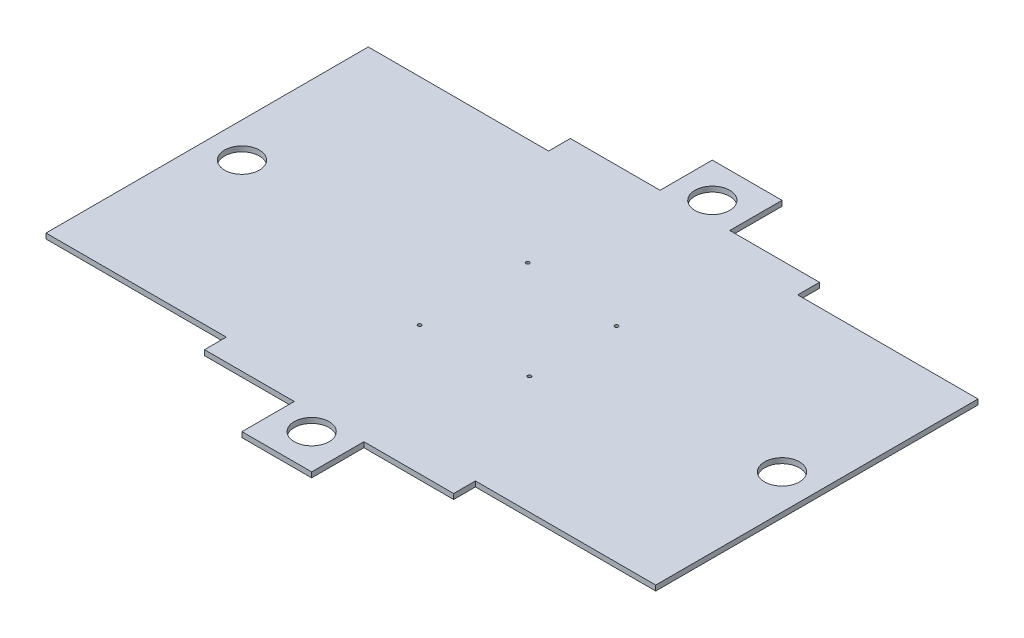
SolidWorks part; units mm, degrees
material "Acrylic (Medium-high impact)"
ref_plane "Front Plane" through (0, 0, 0) normal (0, 0, 1) x (1, 0, 0)
ref_plane "Top Plane" through (0, 0, 0) normal (0, 1, 0) x (1, 0, 0)
ref_plane "Right Plane" through (0, 0, 0) normal (1, 0, 0) x (0, 0, -1)
sketch "Sketch1" plane through (0, 0, 0) normal (0, 1, 0) x (1, 0, 0)
  line L4 (-111.7909, 69.7038) -> (-111.7909, 82.2038)
  line L5 (31.2091, 69.7038) -> (31.2091, 82.2038)
  line L8 (-111.7909, -115.2962) -> (-111.7909, -127.7962)
  line L9 (31.2091, -115.2962) -> (31.2091, -127.7962)
  line L28 (-59.8105, -54.1086) -> (-60.7802, -51.8043)
  line L29 (-60.7802, -51.8043) -> (-63.2606, -51.4919)
  line L30 (-63.2606, -51.4919) -> (-64.7713, -53.4838)
  line L31 (-64.7713, -53.4838) -> (-63.8017, -55.7881)
  line L32 (-63.8017, -55.7881) -> (-61.3213, -56.1005)
  line L33 (-61.3213, -56.1005) -> (-59.8105, -54.1086)
  line L34 (-2.7978, -47.6117) -> (-4.2041, -45.5448)
  line L35 (-4.2041, -45.5448) -> (-6.6973, -45.7293)
  line L36 (-6.6973, -45.7293) -> (-7.7841, -47.9807)
  line L37 (-7.7841, -47.9807) -> (-6.3778, -50.0476)
  line L38 (-6.3778, -50.0476) -> (-3.8846, -49.8631)
  line L39 (-3.8846, -49.8631) -> (-2.7978, -47.6117)
  line L40 (-2.8598, 1.621) -> (-3.5707, 4.0178)
  line L41 (-3.5707, 4.0178) -> (-6.0018, 4.6006)
  line L42 (-6.0018, 4.6006) -> (-7.7221, 2.7866)
  line L43 (-7.7221, 2.7866) -> (-7.0112, 0.3898)
  line L44 (-7.0112, 0.3898) -> (-4.5801, -0.193)
  line L45 (-4.5801, -0.193) -> (-2.8598, 1.621)
  line L46 (-60.0251, 7.1473) -> (-60.2431, 9.6378)
  line L47 (-60.2431, 9.6378) -> (-62.5089, 10.6943)
  line L48 (-62.5089, 10.6943) -> (-64.5567, 9.2603)
  line L49 (-64.5567, 9.2603) -> (-64.3388, 6.7698)
  line L50 (-64.3388, 6.7698) -> (-62.073, 5.7133)
  line L51 (-62.073, 5.7133) -> (-60.0251, 7.1473)
  line L57 (-60.2909, 112.2038) -> (-20.2909, 112.2038)
  line L58 (-20.2909, 112.2038) -> (-20.2909, 82.2038)
  line L65 (-60.2909, -157.7962) -> (-20.2909, -157.7962)
  line L66 (-20.2909, -157.7962) -> (-20.2909, -127.7962)
  line L67 (-111.7909, 82.2038) -> (-60.2909, 82.2038)
  line L68 (31.2091, 82.2038) -> (-20.2909, 82.2038)
  line L69 (31.2091, -127.7962) -> (-20.2909, -127.7962)
  line L70 (-111.7909, -127.7962) -> (-60.2909, -127.7962)
  line L71 (-60.2909, -127.7962) -> (-60.2909, -157.7962)
  line L72 (-60.2909, 82.2038) -> (-60.2909, 112.2038)
  line L78 (31.2091, 69.7038) -> (134.7091, 69.7038)
  line L79 (134.7091, 69.7038) -> (134.7091, -115.2962)
  line L80 (134.7091, -115.2962) -> (31.2091, -115.2962)
  line L81 (-111.7909, -115.2962) -> (-215.2909, -115.2962)
  line L82 (-215.2909, -115.2962) -> (-215.2909, 69.7038)
  line L83 (-215.2909, 69.7038) -> (-111.7909, 69.7038)
  circle A45 centre (-5.2909, -47.7962) radius 1
  circle A46 centre (-5.2909, 2.2038) radius 1
  circle A47 centre (-62.2909, -53.7962) radius 1
  circle A48 centre (-62.2909, 8.2038) radius 1
  circle A50 centre (-40.2909, 92.2038) radius 10
  circle A52 centre (-40.2909, -137.7962) radius 10
  circle A54 centre (114.7091, -22.7962) radius 10
  circle A55 centre (-195.2909, -22.7962) radius 10
  point P48 (-111.7909, 69.7038)
  dimension "D1" = 20
  dimension "D2" = 2
  dimension "D4" = 114.7091
  dimension "D5" = 31.2091
  dimension "D6" = 134.7091
  dimension "D7" = 2.7978
  dimension "D8" = 2.8598
  dimension "D9" = 3.5707
  dimension "D10" = 3.8846
  dimension "D11" = 4.2041
  dimension "D12" = 5.2909
  dimension "D13" = 4.5801
  dimension "D14" = 6.0018
  dimension "D15" = 6.3778
  dimension "D16" = 6.6973
  dimension "D17" = 7.0112
  dimension "D18" = 20.2909
  dimension "D19" = 59.8105
  dimension "D20" = 40.2909
  dimension "D21" = 60.0251
  dimension "D22" = 60.2431
  dimension "D23" = 60.2909
  dimension "D24" = 60.7802
  dimension "D25" = 61.3213
  dimension "D26" = 62.073
  dimension "D27" = 62.5089
  dimension "D28" = 62.2909
  dimension "D29" = 63.2606
  dimension "D30" = 63.8017
  dimension "D31" = 64.3388
  dimension "D32" = 0.3898
  dimension "D33" = 1.621
  dimension "D34" = 2.2038
  dimension "D35" = 5.7133
  dimension "D36" = 195.2909
  dimension "D37" = 69.7038
  dimension "D38" = 82.2038
  dimension "D39" = 112.2038
  dimension "D40" = 45.5448
  dimension "D41" = 51.4919
  dimension "D42" = 8.2038
  dimension "D43" = 115.2962
  dimension "D51" = 22.7962
  dimension "D55" = 47.7962
  dimension "D62" = 53.7962
extrude "Boss-Extrude1" add sketch "Sketch1" along normal blind 3
